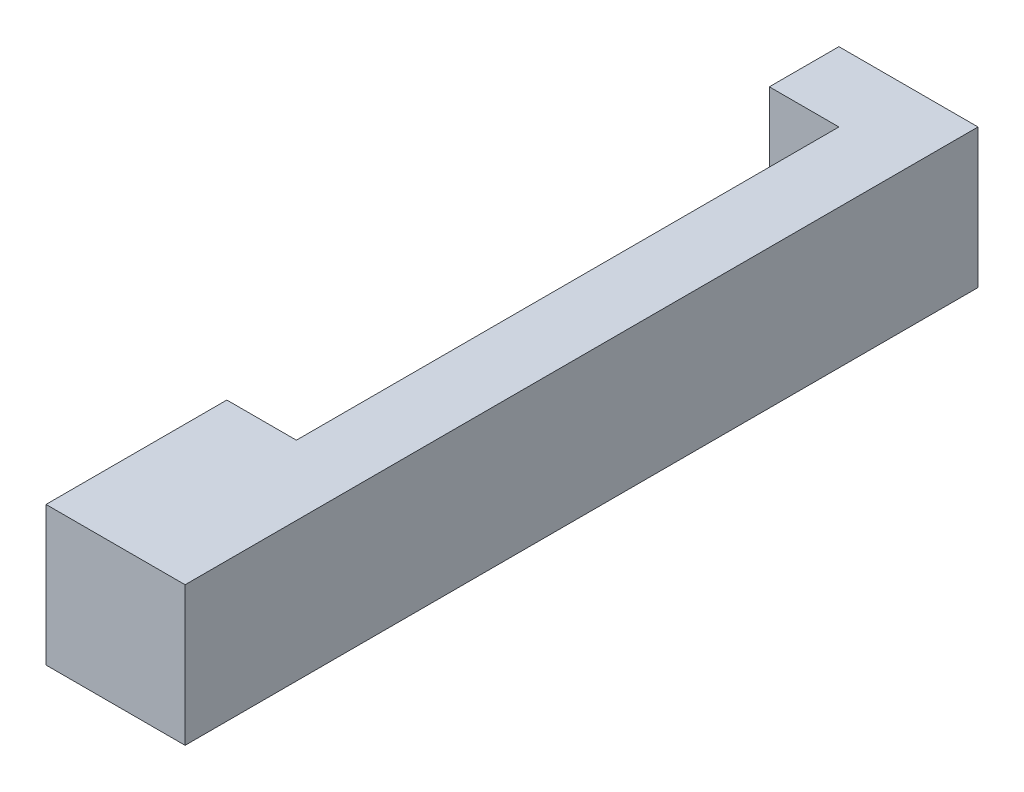
SolidWorks part; units mm, degrees
ref_plane "Front Plane" through (0, 0, 0) normal (0, 0, 1) x (1, 0, 0)
ref_plane "Top Plane" through (0, 0, 0) normal (0, 1, 0) x (1, 0, 0)
ref_plane "Right Plane" through (0, 0, 0) normal (1, 0, 0) x (0, 0, -1)
sketch "Sketch1" plane through (0, 0, 0) normal (0, 1, 0) x (1, 0, 0)
  line L1 (0, 0) -> (-25.4, 0)
  line L2 (0, 0) -> (0, 33.02)
  line L3 (0, 33.02) -> (-25.4, 33.02)
  line L4 (-25.4, 0) -> (-25.4, 33.02)
  line L5 (0, 33.02) -> (-12.7, 33.02)
  line L6 (0, 33.02) -> (0, 144.78)
  line L7 (0, 144.78) -> (-12.7, 144.78)
  line L8 (-12.7, 33.02) -> (-12.7, 144.78)
  line L9 (-12.7, 144.78) -> (-25.4, 144.78)
  line L10 (-12.7, 144.78) -> (-12.7, 132.08)
  line L11 (-12.7, 132.08) -> (-25.4, 132.08)
  line L12 (-25.4, 144.78) -> (-25.4, 132.08)
  dimension "D1" = 33.02
  dimension "D2" = 25.4
  dimension "D3" = 12.7
  dimension "D4" = 25.4
  dimension "D5" = 12.7
  dimension "D6" = 132.08
extrude "Boss-Extrude1" add sketch "Sketch1" along normal blind 25.4 contours L4 L1 L2 L3 | L8 L3 L6 L7 | L9 L12 L11 L10
